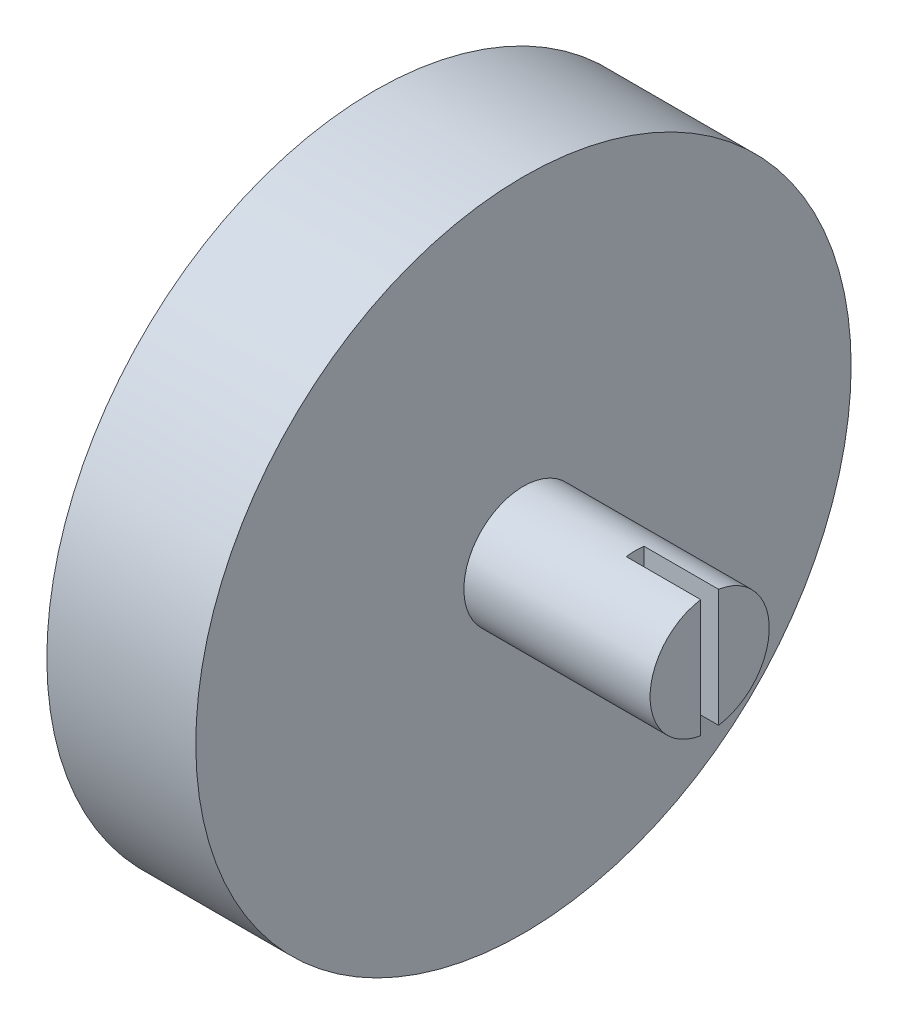
SolidWorks part; units mm, degrees
ref_plane "Front Plane" through (0, 0, 0) normal (0, 0, 1) x (1, 0, 0)
ref_plane "Top Plane" through (0, 0, 0) normal (0, 1, 0) x (1, 0, 0)
ref_plane "Right Plane" through (0, 0, 0) normal (1, 0, 0) x (0, 0, -1)
sketch "Sketch1" plane through (0, 0, 0) normal (1, 0, 0) x (0, 0, -1)
  circle A0 centre (0, 0) radius 22
  dimension "D1" = 44
extrude "Boss-Extrude1" add sketch "Sketch1" along normal blind 10
sketch "Sketch8" plane through (0, 0, 0) normal (1, 0, 0) x (0, 0, -1)
  line L0 (-0.6, -5) -> (0.6, 5) construction
  line L1 (-0.6, 5) -> (0.6, -5) construction
  line L2 (-0.6, -5) -> (0.6, -5)
  line L3 (-0.6, 5) -> (0.6, 5)
  line L4 (-0.6, 5) -> (-0.6, -5)
  line L5 (0.6, -5) -> (0.6, 5)
  point P4 (0, 0)
  dimension "D1" = 1.2
  dimension "D2" = 10
sketch "Sketch13" plane through (0, 0, 0) normal (1, 0, 0) x (0, 0, -1)
  line L0 (-2.6704, -16.8582) -> (-2.6704, -16.5304)
  line L1 (6.5, 19.5569) -> (6.5, -6.9431)
  line L2 (-6.5, 19.5569) -> (-6.5, -6.9431)
  line L3 (0, -25.25) -> (0, 0) construction
  line L4 (2.6704, -16.8582) -> (2.6704, -16.5304)
  line L5 (-4.7624, -10) -> (-2.6704, -16.5304)
  line L6 (0, -25.25) -> (-1.0006, -21.9772)
  line L7 (-6.5, 19.5569) -> (6.5, 19.5569)
  line L8 (-6.5, -6.9431) -> (-4.7624, -6.9431)
  line L9 (6.5, -6.9431) -> (4.7624, -6.9431)
  line L10 (1.0006, -21.9772) -> (0, -25.25)
  line L11 (4.7624, -10) -> (2.6704, -16.5304)
  line L12 (-2.6704, -16.8582) -> (-2.6704, -21.8373)
  line L13 (-4.7624, -10) -> (-4.7624, -6.9431)
  line L14 (4.7624, -10) -> (4.7624, -6.9431)
  line L15 (2.6704, -16.8582) -> (2.6704, -21.8373)
  arc A0 (-2.6704, -21.8373) -> (-1.0006, -21.9772) centre (0, 0) ccw
  arc A1 (1.0006, -21.9772) -> (2.6704, -21.8373) centre (0, 0) ccw
  dimension "D1" = 13
  dimension "D2" = 26.5
  dimension "D3" = 3.0569
  dimension "D4" = 25.25
extrude "Cut-Extrude2" cut sketch "Sketch13" along normal blind 5.5 contours L1 L9 L14 L11 L4 L15 A1 L10 L6 A0 L12 L0 L5 L13 L8 L2 L7
sketch "Sketch15" plane through (0, 0, 0) normal (-1, 0, 0) x (0, 0, 1)
  line L0 (9, 17.1749) -> (9, -6.9431)
  line L1 (9, 17.1749) -> (-9, 17.1749)
  line L2 (9, -6.9431) -> (-9, -6.9431)
  line L3 (0, -6.9431) -> (0, 17.1749) construction
  line L4 (-9, -6.9431) -> (-9, 17.1749)
  line L5 (-6.5, -6.9431) -> (-4.7624, -6.9431) construction
  point P4 (0, -6.9431)
  point P7 (0, 17.1749)
  dimension "D1" = 18
  dimension "D2" = 24.118
extrude "Cut-Extrude3" cut sketch "Sketch15" against normal blind 3
sketch "Sketch16" plane through (10, 0, 0) normal (1, 0, 0) x (0, 0, -1)
  circle A0 centre (0, 0) radius 4
  dimension "D1" = 8
extrude "Boss-Extrude2" add sketch "Sketch16" along normal blind 12.5
extrude "Cut-Extrude4" cut sketch "Sketch8" against normal blind 5 from offset 22.5
sketch "Sketch17" plane through (0, -6.9431, 0) normal (0, 1, 0) x (1, 0, 0)
  line L0 (0, 4.7624) -> (0, 6.5124)
  line L1 (0, 9) -> (0, 4.7624) construction
  line L2 (0, 6.5124) -> (4, 6.5124)
  line L3 (4, 6.5124) -> (4, 4.7624)
  line L4 (5.5, 4.7624) -> (0, 4.7624) construction
  line L5 (4, 4.7624) -> (0, 4.7624)
  dimension "D1" = 1.75
  dimension "D2" = 4
extrude "Boss-Extrude3" add sketch "Sketch17" along normal blind 1
sketch "Sketch18" plane through (0, -6.9431, 0) normal (0, 1, 0) x (1, 0, 0)
  line L0 (5.5, -6.5) -> (3, -6.5) construction
  line L1 (0, -4.7624) -> (4.25, -4.7624)
  line L2 (0, -4.7624) -> (0, -6.5)
  line L3 (0, -6.5) -> (4.25, -6.5)
  line L4 (4.25, -4.7624) -> (4.25, -6.5)
  dimension "D1" = 1.7376
extrude "Boss-Extrude4" add sketch "Sketch18" along normal blind 1
sketch "Sketch22" plane through (0, 0, 0) normal (1, 0, 0) x (0, 0, -1)
  line L0 (0, 0) -> (0, 16.8191) construction
  circle A0 centre (-14, 0) radius 1.5
  circle A1 centre (14, 0) radius 1.5
  dimension "D1" = 3
  dimension "D2" = 14
extrude "Cut-Extrude7" cut sketch "Sketch22" along normal blind 7 from surface at 0 starting at face at (0, 0.1685, -0.0012)
